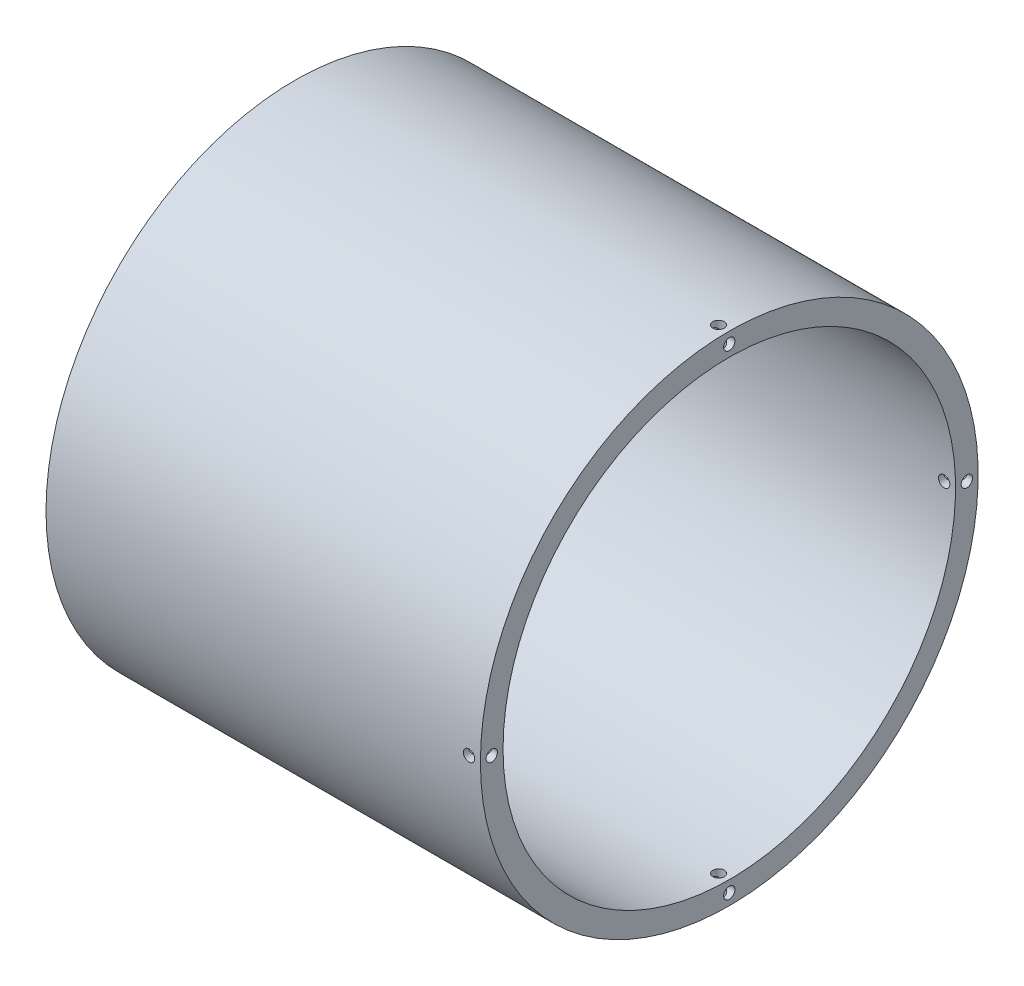
SolidWorks part; units mm, degrees
ref_plane "Front Plane" through (0, 0, 0) normal (0, 0, 1) x (1, 0, 0)
ref_plane "Top Plane" through (0, 0, 0) normal (0, 1, 0) x (1, 0, 0)
ref_plane "Right Plane" through (0, 0, 0) normal (1, 0, 0) x (0, 0, -1)
sketch "Sketch1" plane through (0, 0, 0) normal (0, 0, 1) x (1, 0, 0)
  line L0 (0, 0) -> (31.2358, 0) construction
  line L1 (0, 0) -> (0, 50) construction
  line L2 (0, 50) -> (0, 55)
  line L3 (0, 55) -> (96, 55)
  line L4 (96, 55) -> (96, 50)
  line L5 (96, 50) -> (0, 50)
  dimension "D1" = 50
  dimension "D2" = 96
  dimension "D3" = 5
revolve "Revolve1" add sketch "Sketch1" angle 360 about L0
sketch "Sketch2" plane through (0, 0, 0) normal (0, 1, 0) x (1, 0, 0)
  line L0 (96, 0) -> (0, 0) construction
  circle A0 centre (93.6372, 0) radius 1.25
  dimension "D1" = 2.5
extrude "Cut-Extrude1" cut sketch "Sketch2" along normal through all both and the other way through all
sketch "Sketch4" plane through (0, 0, 0) normal (0, 0, 1) x (1, 0, 0)
  circle A0 centre (93.4815, 0) radius 1.25
  dimension "D1" = 2.5
extrude "Cut-Extrude2" cut sketch "Sketch4" against normal through all both and the other way through all
sketch "Sketch5" plane through (96, 0, 0) normal (1, 0, 0) x (0, 0, -1)
  line L0 (0, 55) -> (0, 50) construction
  circle A0 centre (0, 0) radius 55 construction
  circle A1 centre (0, 0) radius 50 construction
  circle A2 centre (0, 52.5) radius 1.25
  dimension "D1" = 2.5
extrude "Cut-Extrude3" cut sketch "Sketch5" against normal blind 5
pattern_circular "CirPattern1" count 4 over 360 about axis through (0, 0, 0) along (1, 0, 0) of "Cut-Extrude3"
